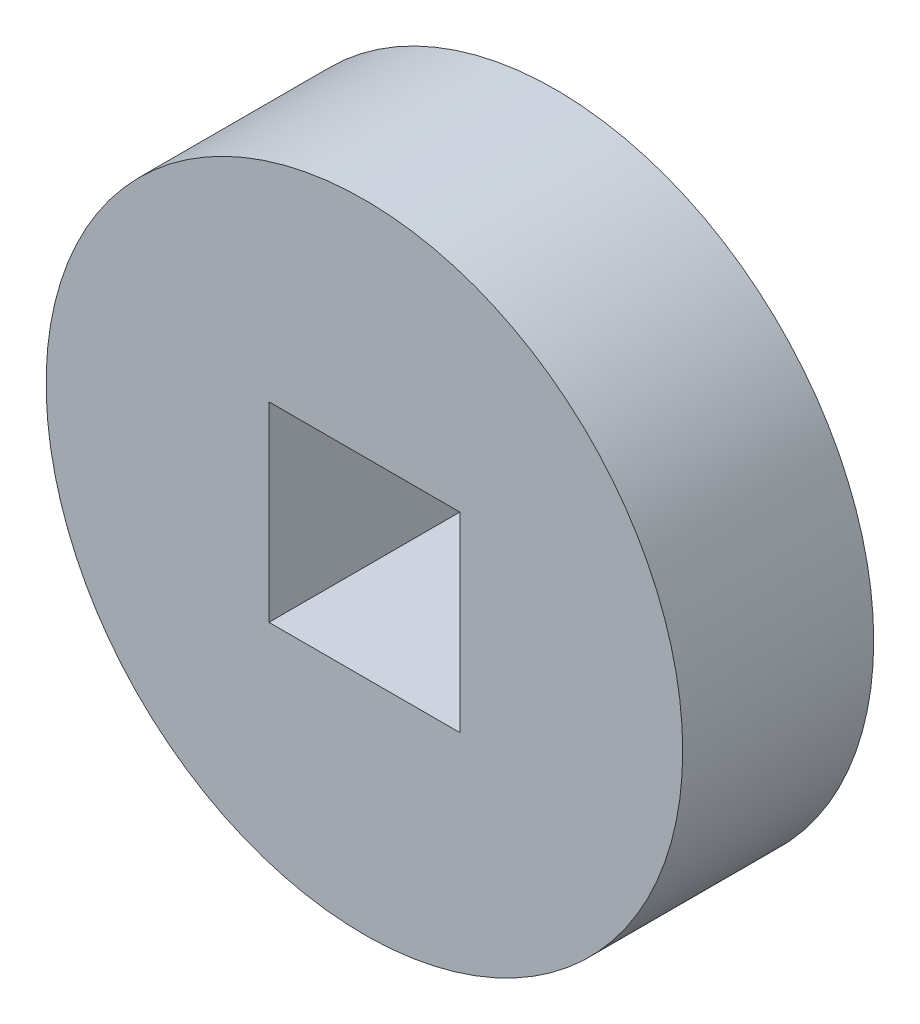
SolidWorks part; units mm, degrees
ref_plane "Front Plane" through (0, 0, 0) normal (0, 0, 1) x (1, 0, 0)
ref_plane "Top Plane" through (0, 0, 0) normal (0, 1, 0) x (1, 0, 0)
ref_plane "Right Plane" through (0, 0, 0) normal (1, 0, 0) x (0, 0, -1)
sketch "Sketch2" plane through (0, 0, 0) normal (0, 0, 1) x (1, 0, 0)
  line L1 (-1.5, 1.5) -> (1.5, 1.5)
  line L2 (-1.5, 1.5) -> (-1.5, -1.5)
  line L3 (-1.5, -1.5) -> (1.5, -1.5)
  line L4 (1.5, 1.5) -> (1.5, -1.5)
  circle A0 centre (0, 0) radius 5
  dimension "D5" = 10
  dimension "D1" = 3
  dimension "D2" = 3
  dimension "D3" = 1.5
  dimension "D4" = 1.5
extrude "Boss-Extrude2" add sketch "Sketch2" along normal blind 3
